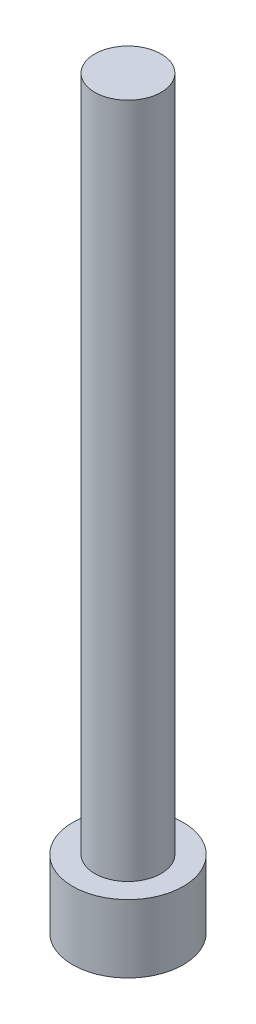
SolidWorks part; units mm, degrees
ref_plane "Front Plane" through (0, 0, 0) normal (0, 0, 1) x (1, 0, 0)
ref_plane "Top Plane" through (0, 0, 0) normal (0, 1, 0) x (1, 0, 0)
ref_plane "Right Plane" through (0, 0, 0) normal (1, 0, 0) x (0, 0, -1)
sketch "Sketch1" plane through (0, 0, 0) normal (0, 1, 0) x (1, 0, 0)
  circle A0 centre (0, 0) radius 2.8575
  dimension "D1" = 5.715
extrude "Boss-Extrude1" add sketch "Sketch1" along normal blind 3.5052
sketch "Sketch2" plane through (0, 0, 0) normal (0, -1, 0) x (1, 0, 0)
  line L1 (1.604, 0) -> (0.802, 1.3891)
  line L2 (0.802, 1.3891) -> (-0.802, 1.3891)
  line L3 (-0.802, 1.3891) -> (-1.604, 0)
  line L4 (-1.604, 0) -> (-0.802, -1.3891)
  line L5 (-0.802, -1.3891) -> (0.802, -1.3891)
  line L6 (0.802, -1.3891) -> (1.604, 0)
  circle A0 centre (0, 0) radius 1.3891 construction
  dimension "D1" = 2.7781
extrude "Cut-Extrude1" cut sketch "Sketch2" against normal blind 1.9558
sketch "Sketch3" plane through (0, 3.5052, 0) normal (0, 1, 0) x (1, 0, 0)
  circle A0 centre (0, 0) radius 1.7145
  dimension "D1" = 3.429
extrude "Boss-Extrude2" add sketch "Sketch3" along normal blind 34.925
